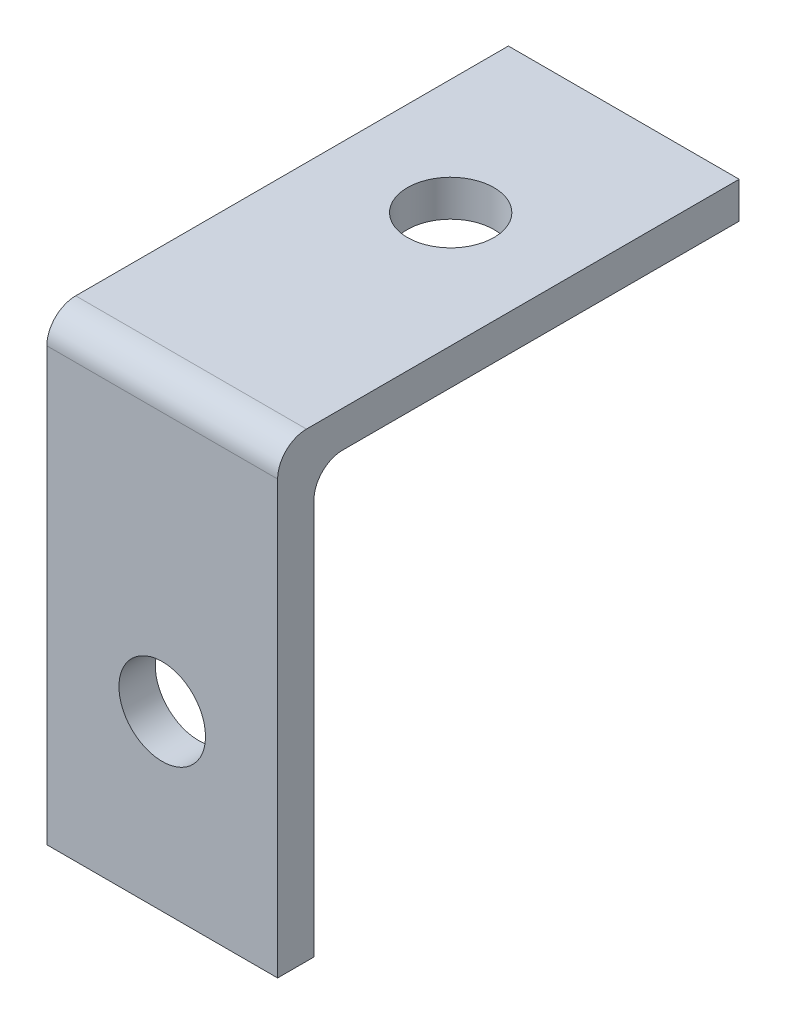
SolidWorks part; units mm, degrees
ref_plane "Alzado" through (0, 0, 0) normal (0, 0, 1) x (1, 0, 0)
ref_plane "Planta" through (0, 0, 0) normal (0, 1, 0) x (1, 0, 0)
ref_plane "Vista lateral" through (0, 0, 0) normal (1, 0, 0) x (0, 0, -1)
sketch "Croquis1" plane through (0, 0, 0) normal (0, 1, 0) x (1, 0, 0)
  line L1 (-6.35, 12.7) -> (6.35, 12.7)
  line L2 (-6.35, 12.7) -> (-6.35, -12.7)
  line L3 (-6.35, -12.7) -> (6.35, -12.7)
  line L4 (6.35, 12.7) -> (6.35, -12.7)
  line L5 (-6.35, 12.7) -> (6.35, -12.7) construction
  line L6 (-6.35, -12.7) -> (6.35, 12.7) construction
  point P0 (0, 0)
  dimension "D1" = 12.7
  dimension "D2" = 25.4
extrude "Saliente-Extruir1" add sketch "Croquis1" along normal blind 2
sketch "Croquis2" plane through (0, 0, 0) normal (0, -1, 0) x (1, 0, 0)
  line L0 (6.35, 12.7) -> (6.35, -12.7) construction
  line L1 (-6.35, 12.7) -> (6.35, 12.7)
  line L2 (-6.35, 12.7) -> (-6.35, 10.7)
  line L3 (-6.35, 10.7) -> (6.35, 10.7)
  line L4 (6.35, 12.7) -> (6.35, 10.7)
  dimension "D1" = 2
extrude "Saliente-Extruir2" add sketch "Croquis2" along normal blind 23.368
fillet "Redondeo1" radius 1.5875 2 edges at (0, 0, 10.7) (0, 2, 12.7)
ref_plane "Plano1" through (0, 0, 0) normal (1, 0, 0) x (0, 0, -1)
sketch "Croquis3" plane through (0, 2, 0) normal (0, 1, 0) x (1, 0, 0)
  line L0 (-6.35, 12.7) -> (-6.35, -6.35) construction
  line L1 (-6.35, 12.7) -> (-6.35, -11.1125) construction
  line L2 (-6.35, -6.35) -> (6.35, -6.35) construction
  line L3 (6.35, -11.1125) -> (6.35, 12.7) construction
  line L4 (0, -6.35) -> (0, 12.7) construction
  line L5 (0, -19.9683) -> (0, 19.9683) construction
  line L6 (-6.35, 3.175) -> (6.35, 3.175) construction
  circle A0 centre (0, 3.175) radius 2.3813
  dimension "D2" = 4.7625
  dimension "D1" = 19.05
extrude "Cortar-Extruir1" cut sketch "Croquis3" against normal through all
sketch "Croquis4" plane through (0, 0, 12.7) normal (0, 0, 1) x (1, 0, 0)
  line L0 (-6.35, -23.368) -> (-6.35, -4.318) construction
  line L1 (-6.35, 0.4125) -> (-6.35, -23.368) construction
  line L2 (-6.35, -4.318) -> (6.35, -6.35) construction
  line L3 (0, 2) -> (0, -25.4) construction
  line L4 (-6.35, 2) -> (6.35, 2) construction
  line L5 (0, -19.9683) -> (0, 19.9683) construction
  line L6 (-6.35, -13.843) -> (6.35, -13.843) construction
  line L7 (6.35, 0.4125) -> (6.35, -23.368) construction
  circle A0 centre (0, -13.843) radius 2.3812
  dimension "D2" = 4.7625
  dimension "D1" = 19.05
extrude "Cortar-Extruir2" cut sketch "Croquis4" against normal blind 2.54
